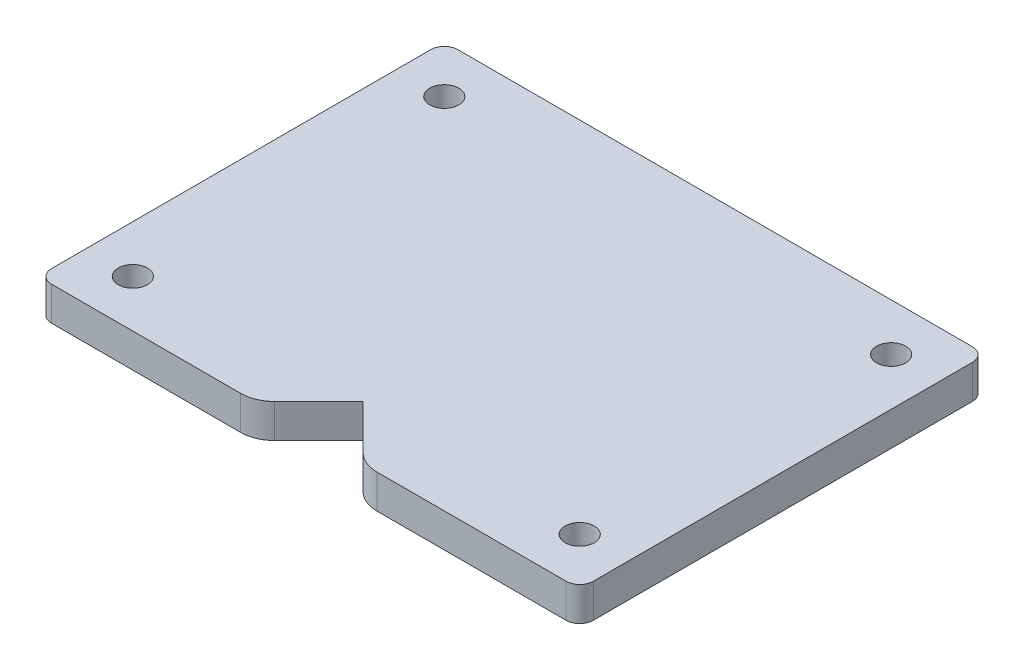
SolidWorks part; units mm, degrees
ref_plane "Front Plane" through (0, 0, 0) normal (0, 0, 1) x (1, 0, 0)
ref_plane "Top Plane" through (0, 0, 0) normal (0, 1, 0) x (1, 0, 0)
ref_plane "Right Plane" through (0, 0, 0) normal (1, 0, 0) x (0, 0, -1)
sketch "Sketch1" plane through (0, 0, 0) normal (0, 0, 1) x (1, 0, 0)
  line L0 (-40, 15.05) -> (40, 15.05)
  line L1 (0, 0) -> (0, 30.1) construction
  line L2 (-40, 15.05) -> (-40, 10.05)
  line L3 (-40, 10.05) -> (-9.7467, 10.05)
  line L4 (40, 15.05) -> (40, 10.05)
  line L5 (40, 10.05) -> (9.7467, 10.05)
  circle A0 centre (0, 0) radius 5.25
  arc A1 (-9.7467, 10.05) -> (9.7467, 10.05) centre (0, 0) ccw
  point P5 (0, 15.05)
  dimension "D1" = 10.5
  dimension "D3" = 15.05
  dimension "D4" = 28
  dimension "D2" = 80
  dimension "D5" = 5
  dimension "D6" = 5
extrude "Boss-Extrude1" add sketch "Sketch1" along normal blind 60
sketch "Sketch2" plane through (0, 0, 0) normal (0, 0, -1) x (-1, 0, 0)
  circle A0 centre (0, 0) radius 11.425
  dimension "D1" = 22.85
extrude "Cut-Extrude1" cut sketch "Sketch2" against normal blind 8.6
sketch "Sketch3" plane through (0, 0, 0) normal (0, 0, -1) x (-1, 0, 0)
  circle A0 centre (0, 0) radius 14
extrude "Cut-Extrude2" cut sketch "Sketch3" against normal blind 5
sketch "Sketch4" plane through (0, 0, 8.6) normal (0, 0, -1) x (-1, 0, 0)
  line L0 (0, 0) -> (0, 17.1857) construction
  line L1 (0, 0) -> (16.2997, 16.2997) construction
  circle A0 centre (0, 0) radius 8 construction
  circle A1 centre (5.6569, 5.6569) radius 1.3
  circle A2 centre (5.6569, -5.6569) radius 1.3
  circle A3 centre (-5.6569, -5.6569) radius 1.3
  circle A4 centre (-5.6569, 5.6569) radius 1.3
  point P16 (0, 0)
  dimension "D2" = 2.6
  dimension "D3" = 16
  dimension "D1" = 45
  dimension "D4" = 4
extrude "Cut-Extrude3" cut sketch "Sketch4" against normal blind 5
sketch "Sketch6" plane through (0, 10.05, 0) normal (0, -1, 0) x (-1, 0, 0)
  line L0 (33, -60) -> (33, 0) construction
  line L1 (40, 0) -> (9.7467, 0) construction
  line L2 (-33, -60) -> (-33, 0) construction
  line L3 (-9.7467, -60) -> (-40, -60) construction
  line L4 (-9.7467, 0) -> (-40, 0) construction
  line L5 (40, -60) -> (40, 0) construction
  line L6 (-40, -60) -> (-40, 0) construction
  line L7 (40, -60) -> (9.7467, -60) construction
  circle A0 centre (33, -53) radius 2.15
  circle A1 centre (33, -7) radius 2.15
  circle A2 centre (-33, -53) radius 2.15
  circle A3 centre (-33, -7) radius 2.15
  dimension "D3" = 4.3
  dimension "D4" = 4.3
  dimension "D5" = 4.3
  dimension "D6" = 4.3
  dimension "D7" = 7
  dimension "D8" = 7
  dimension "D9" = 7
  dimension "D10" = 7
  dimension "D1" = 7
  dimension "D2" = 7
extrude "Cut-Extrude5" cut sketch "Sketch6" against normal through all
sketch "Sketch7" plane through (0, 0, 60) normal (0, 0, 1) x (1, 0, 0)
  line L0 (-9.7467, 10.05) -> (9.7467, 10.05)
  arc A0 (-9.7467, 10.05) -> (9.7467, 10.05) centre (0, 0) ccw
extrude "Cut-Extrude6" cut sketch "Sketch7" against normal blind 35
fillet "Fillet2" radius 5 2 edges at (-9.7467, 10.05, 15) (9.7467, 10.05, 15)
fillet "Fillet3" radius 2 4 edges at (40, 12.55, 0) (-40, 12.55, 0) (-40, 12.55, 60) (40, 12.55, 60)
fillet "Fillet4" radius 5 1 edges at (0, 10.05, 25)
sketch "Sketch8" plane through (0, 15.05, 0) normal (0, 1, 0) x (1, 0, 0)
  line L0 (0, 0) -> (0, -60) construction
  line L1 (38, -60) -> (-38, -60) construction
  line L2 (0, -52) -> (8, -60)
  line L3 (8, -60) -> (-8, -60)
  line L4 (-8, -60) -> (0, -52)
  dimension "D1" = 45
  dimension "D2" = 45
  dimension "D3" = 8
extrude "Cut-Extrude7" cut sketch "Sketch8" against normal through all
fillet "Fillet5" radius 5 2 edges at (8, 12.55, 60) (-8, 12.55, 60)
